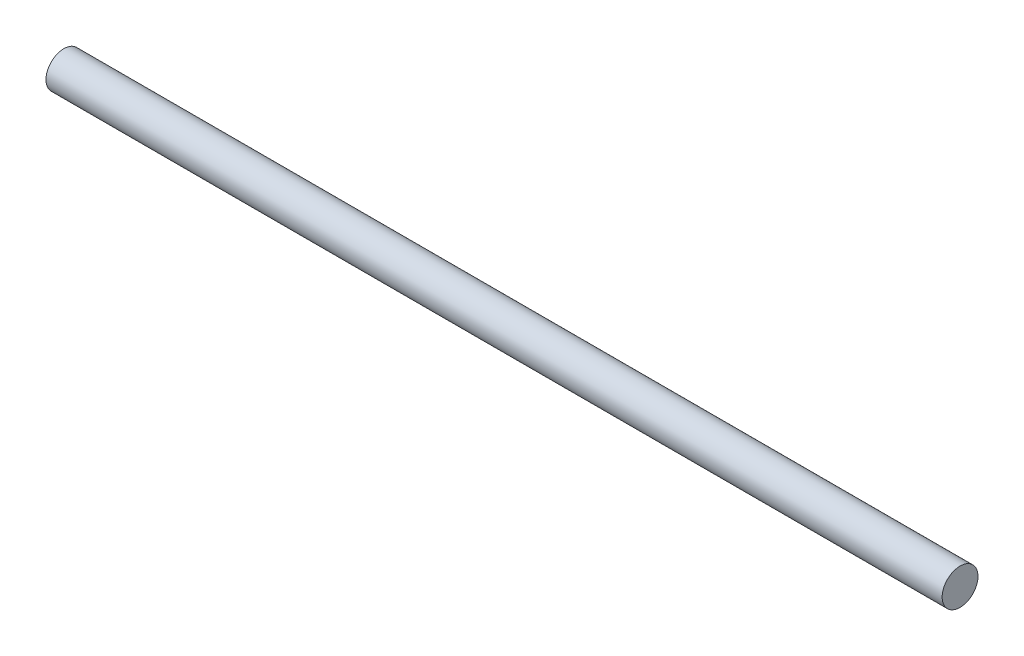
SolidWorks part; units mm, degrees
material "Stainless Steel (ferritic)"
ref_plane "Front Plane" through (0, 0, 0) normal (0, 0, 1) x (1, 0, 0)
ref_plane "Top Plane" through (0, 0, 0) normal (0, 1, 0) x (1, 0, 0)
ref_plane "Right Plane" through (0, 0, 0) normal (1, 0, 0) x (0, 0, -1)
sketch "Sketch2" plane through (0, 0, 0) normal (1, 0, 0) x (0, 0, -1)
  circle A0 centre (0, 0) radius 10
  dimension "D1" = 20
extrude "Boss-Extrude1" add sketch "Sketch2" along normal blind 500
